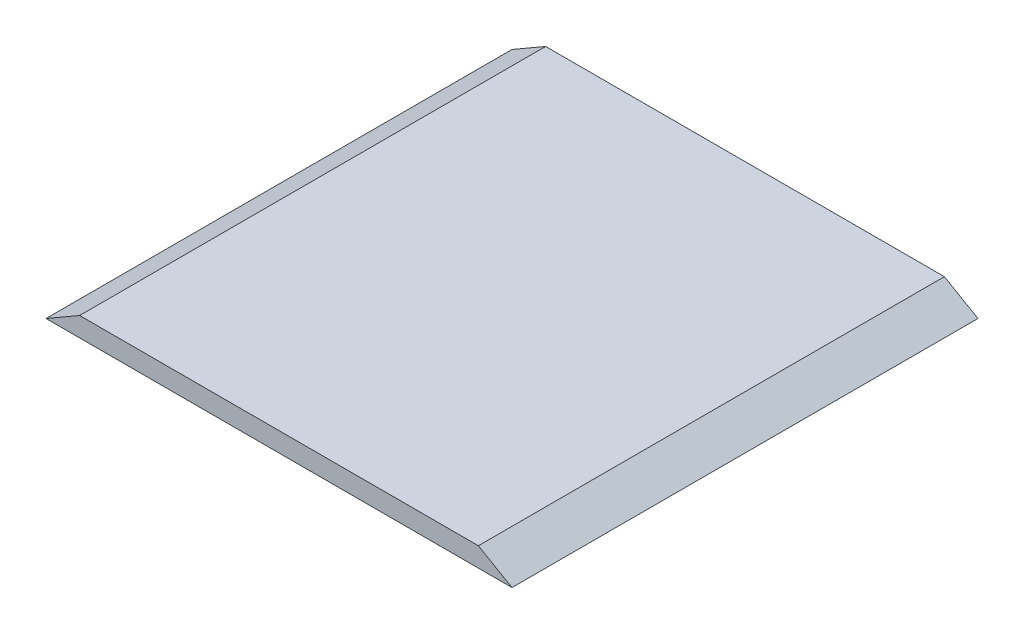
SolidWorks part; units mm, degrees
ref_plane "Front Plane" through (0, 0, 0) normal (0, 0, 1) x (1, 0, 0)
ref_plane "Top Plane" through (0, 0, 0) normal (0, 1, 0) x (1, 0, 0)
ref_plane "Right Plane" through (0, 0, 0) normal (1, 0, 0) x (0, 0, -1)
sketch "Sketch1" plane through (0, 0, 0) normal (0, 1, 0) x (1, 0, 0)
  line L1 (0, 0) -> (304.8, 0)
  line L2 (0, 0) -> (0, -304.8)
  line L3 (0, -304.8) -> (304.8, -304.8)
  line L4 (304.8, 0) -> (304.8, -304.8)
extrude "Boss-Extrude1" add sketch "Sketch1" along normal blind 12.7
sketch "Sketch2" plane through (0, 0, 304.8) normal (0, 0, 1) x (1, 0, 0)
  line L0 (0, 0) -> (21.997, 12.7)
  line L1 (0, 12.7) -> (304.8, 12.7) construction
  line L2 (304.8, 0) -> (282.803, 12.7)
  line L3 (0, 12.7) -> (0, 0) construction
  line L4 (0, 0) -> (0, 12.7)
  line L5 (0, 12.7) -> (21.997, 12.7)
  line L6 (304.8, 0) -> (304.8, 12.7)
  line L7 (304.8, 12.7) -> (282.803, 12.7)
  arc A0 (0, 7.1819) -> (6.2198, 3.591) centre (0, 0) cw construction
extrude "Cut-Extrude1" cut sketch "Sketch2" against normal through all
sketch "Sketch3" plane through (0, 12.7, 0) normal (0, 1, 0) x (1, 0, 0)
  line L0 (21.997, -12.7) -> (282.803, -12.7)
  line L1 (21.997, 0) -> (21.997, -304.8) construction
  line L2 (282.803, 0) -> (282.803, -304.8) construction
  line L3 (21.997, -292.1) -> (282.803, -292.1)
  line L4 (152.4, -292.1) -> (152.4, -304.8) construction
  line L5 (21.997, -304.8) -> (282.803, -304.8) construction
  line L6 (152.4, -12.7) -> (152.4, 0) construction
  line L7 (282.803, 0) -> (21.997, 0) construction
